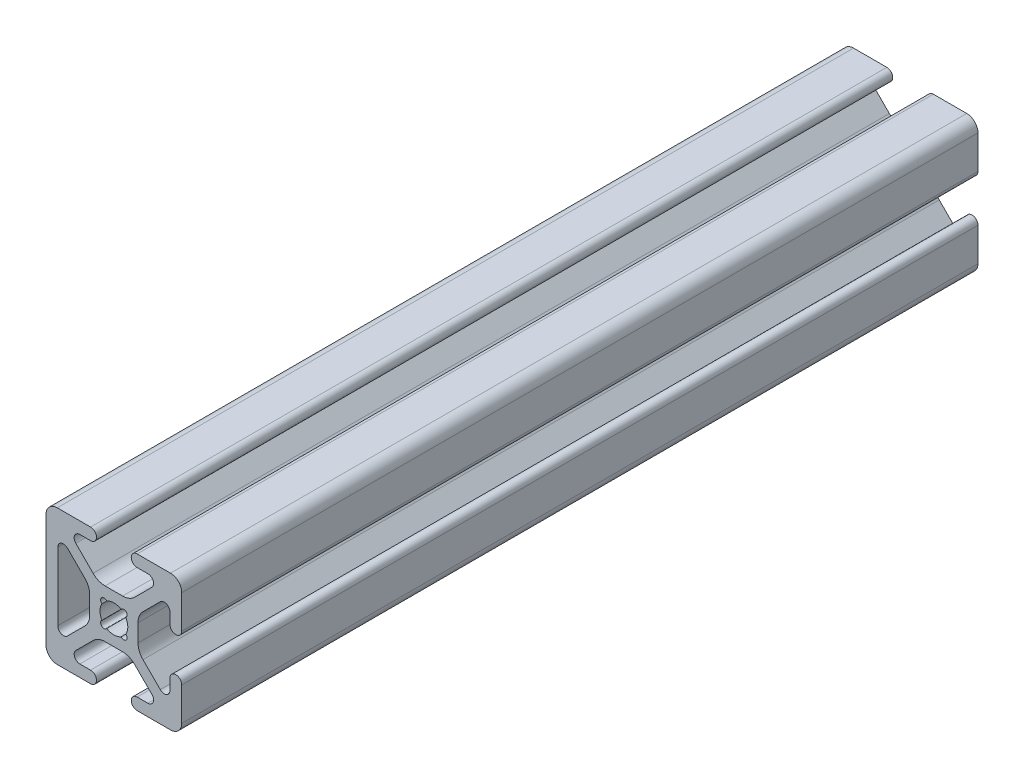
SolidWorks part; units mm, degrees
ref_plane "Front Plane" through (0, 0, 0) normal (0, 0, 1) x (1, 0, 0)
ref_plane "Top Plane" through (0, 0, 0) normal (0, 1, 0) x (1, 0, 0)
ref_plane "Right Plane" through (0, 0, 0) normal (1, 0, 0) x (0, 0, -1)
ref_plane "Plane1" through (0, 0, 12.7) normal (0, 0, 1) x (1, 0, 0)
sketch "Sketch1" plane through (0, 0, 12.7) normal (0, 0, 1) x (1, 0, 0)
  line L0 (-8.6817, 7.1192) -> (-5.4471, 3.8846)
  line L1 (-4.5172, 1.6396) -> (-4.5172, -1.6396)
  line L2 (-5.4471, -3.8846) -> (-8.6817, -7.1192)
  line L3 (-10.4902, -6.3701) -> (-10.4902, 6.3701)
  line L4 (-12.7, 10.5918) -> (-12.7, -10.5918)
  line L5 (-10.5918, -12.7) -> (-4.3561, -12.7)
  line L6 (-4.3561, -10.4902) -> (-6.3701, -10.4902)
  line L7 (-7.1192, -8.6817) -> (-3.8846, -5.4471)
  line L8 (-1.6396, -4.5172) -> (1.6396, -4.5172)
  line L9 (3.8846, -5.4471) -> (7.1192, -8.6817)
  line L10 (6.3701, -10.4902) -> (4.3561, -10.4902)
  line L11 (4.3561, -12.7) -> (10.5918, -12.7)
  line L12 (12.7, -10.5918) -> (12.7, -4.3561)
  line L13 (10.4902, -4.3561) -> (10.4902, -6.3701)
  line L14 (8.6817, -7.1192) -> (5.4471, -3.8846)
  line L15 (4.5172, -1.6396) -> (4.5172, 1.6396)
  line L16 (5.4471, 3.8846) -> (8.6817, 7.1192)
  line L17 (10.4902, 6.3701) -> (10.4902, 4.3561)
  line L18 (12.7, 4.3561) -> (12.7, 10.5918)
  line L19 (10.5918, 12.7) -> (4.3561, 12.7)
  line L20 (4.3561, 10.4902) -> (6.3701, 10.4902)
  line L21 (7.1192, 8.6817) -> (3.8846, 5.4471)
  line L22 (1.6396, 4.5172) -> (-1.6396, 4.5172)
  line L23 (-3.8846, 5.4471) -> (-7.1192, 8.6817)
  line L24 (-6.3701, 10.4902) -> (-4.3561, 10.4902)
  line L25 (-4.3561, 12.7) -> (-10.5918, 12.7)
  arc A0 (-10.4902, 6.3701) -> (-8.6817, 7.1192) centre (-9.4308, 6.3701) cw
  arc A1 (-5.4471, 3.8846) -> (-4.5172, 1.6396) centre (-7.6922, 1.6396) cw
  arc A2 (-4.5172, -1.6396) -> (-5.4471, -3.8846) centre (-7.6922, -1.6396) cw
  arc A3 (-8.6817, -7.1192) -> (-10.4902, -6.3701) centre (-9.4308, -6.3701) cw
  arc A4 (-2.2319, 1.3405) -> (-1.3405, 2.2319) centre (-1.841, 1.841) cw
  arc A5 (-1.3405, 2.2319) -> (1.3405, 2.2319) centre (0, 0) cw
  arc A6 (1.3405, 2.2319) -> (2.2319, 1.3405) centre (1.841, 1.841) cw
  arc A7 (2.2319, 1.3405) -> (2.2319, -1.3405) centre (0, 0) cw
  arc A8 (2.2319, -1.3405) -> (1.3405, -2.2319) centre (1.841, -1.841) cw
  arc A9 (1.3405, -2.2319) -> (-1.3405, -2.2319) centre (0, 0) cw
  arc A10 (-1.3405, -2.2319) -> (-2.2319, -1.3405) centre (-1.841, -1.841) cw
  arc A11 (-2.2319, -1.3405) -> (-2.2319, 1.3405) centre (0, 0) cw
  arc A12 (-10.5918, 12.7) -> (-12.7, 10.5918) centre (-10.5918, 10.5918) ccw
  arc A13 (-12.7, -10.5918) -> (-10.5918, -12.7) centre (-10.5918, -10.5918) ccw
  arc A14 (-4.3561, -12.7) -> (-4.3561, -10.4902) centre (-4.3561, -11.5951) ccw
  arc A15 (-6.3701, -10.4902) -> (-7.1192, -8.6817) centre (-6.3701, -9.4308) cw
  arc A16 (-3.8846, -5.4471) -> (-1.6396, -4.5172) centre (-1.6396, -7.6922) cw
  arc A17 (1.6396, -4.5172) -> (3.8846, -5.4471) centre (1.6396, -7.6922) cw
  arc A18 (7.1192, -8.6817) -> (6.3701, -10.4902) centre (6.3701, -9.4308) cw
  arc A19 (4.3561, -10.4902) -> (4.3561, -12.7) centre (4.3561, -11.5951) ccw
  arc A20 (10.5918, -12.7) -> (12.7, -10.5918) centre (10.5918, -10.5918) ccw
  arc A21 (12.7, -4.3561) -> (10.4902, -4.3561) centre (11.5951, -4.3561) ccw
  arc A22 (10.4902, -6.3701) -> (8.6817, -7.1192) centre (9.4308, -6.3701) cw
  arc A23 (5.4471, -3.8846) -> (4.5172, -1.6396) centre (7.6922, -1.6396) cw
  arc A24 (4.5172, 1.6396) -> (5.4471, 3.8846) centre (7.6922, 1.6396) cw
  arc A25 (8.6817, 7.1192) -> (10.4902, 6.3701) centre (9.4308, 6.3701) cw
  arc A26 (10.4902, 4.3561) -> (12.7, 4.3561) centre (11.5951, 4.3561) ccw
  arc A27 (12.7, 10.5918) -> (10.5918, 12.7) centre (10.5918, 10.5918) ccw
  arc A28 (4.3561, 12.7) -> (4.3561, 10.4902) centre (4.3561, 11.5951) ccw
  arc A29 (6.3701, 10.4902) -> (7.1192, 8.6817) centre (6.3701, 9.4308) cw
  arc A30 (3.8846, 5.4471) -> (1.6396, 4.5172) centre (1.6396, 7.6922) cw
  arc A31 (-1.6396, 4.5172) -> (-3.8846, 5.4471) centre (-1.6396, 7.6922) cw
  arc A32 (-7.1192, 8.6817) -> (-6.3701, 10.4902) centre (-6.3701, 9.4308) cw
  arc A33 (-4.3561, 10.4902) -> (-4.3561, 12.7) centre (-4.3561, 11.5951) ccw
extrude "Boss-Extrude1" add sketch "Sketch1" against normal blind 149
